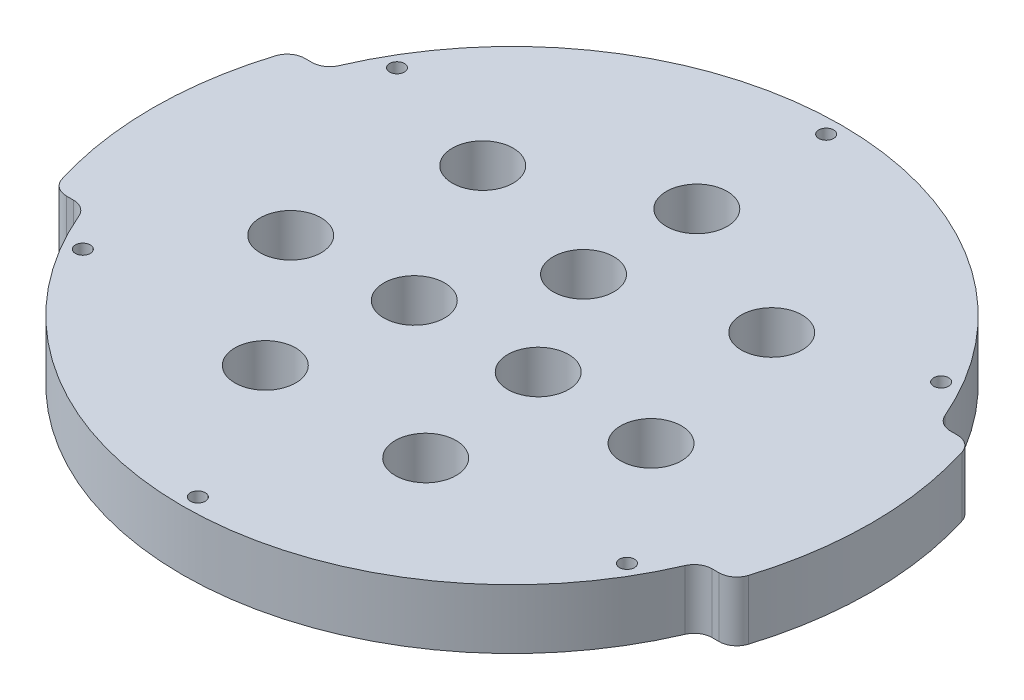
SolidWorks part; units mm, degrees
ref_plane "前视" through (0, 0, 0) normal (0, 0, 1) x (1, 0, 0)
ref_plane "上视" through (0, 0, 0) normal (0, 1, 0) x (1, 0, 0)
ref_plane "右视" through (0, 0, 0) normal (1, 0, 0) x (0, 0, -1)
sketch "草图3" plane through (0, 0, 0) normal (0, 1, 0) x (1, 0, 0)
  circle A0 centre (0, 0) radius 60.3
extrude "凸台-拉伸2" add sketch "草图3" along normal blind 10
sketch "草图4" plane through (0, 10, 0) normal (0, 1, 0) x (1, 0, 0)
  line L0 (-75.2656, 20) -> (82.2187, 20) construction
  line L1 (80.5383, -20) -> (-108.875, -20) construction
  line L2 (-51.5567, 20) -> (-56.8866, 20)
  line L3 (51.5567, 20) -> (56.8866, 20)
  line L4 (-56.8866, -20) -> (-51.5567, -20)
  line L5 (51.5567, -20) -> (56.8866, -20)
  arc A0 (51.5567, 20) -> (-51.5567, 20) centre (0, 0) ccw
  arc A1 (56.8866, 20) -> (-56.8866, 20) centre (0, 0) ccw
  circle A2 centre (0, 0) radius 60.3 construction
  arc A3 (-51.5567, -20) -> (51.5567, -20) centre (0, 0) ccw
  arc A4 (-56.8866, -20) -> (56.8866, -20) centre (0, 0) ccw
  dimension "D1" = 20
  dimension "D2" = 20
extrude "切除-拉伸2" cut sketch "草图4" against normal through all
fillet "圆角1" radius 3 8 edges at (51.5567, 5, -20) (56.8866, 5, -20) (56.8866, 5, 20) (51.5567, 5, 20) (-51.5567, 5, 20) (-56.8866, 5, 20) (-56.8866, 5, -20) (-51.5567, 5, -20)
sketch "草图5" plane through (0, 0, 0) normal (0, -1, 0) x (1, 0, 0)
  circle A0 centre (0, -52.7) radius 1.25
  arc A1 (-50.8147, -21.8165) -> (50.8147, -21.8165) centre (0, 0) ccw construction
  circle A2 centre (-45.6395, -26.35) radius 1.25
  circle A3 centre (-45.6395, 26.35) radius 1.25
  circle A4 centre (0, 52.7) radius 1.25
  circle A5 centre (45.6395, 26.35) radius 1.25
  circle A6 centre (45.6395, -26.35) radius 1.25
  point P2 (0, -55.3)
  point P19 (0, 0)
  dimension "D2" = 2.5
  dimension "D1" = 2.6
  dimension "D3" = 6
extrude "切除-拉伸3" cut sketch "草图5" against normal through all
sketch "草图6" plane through (0, 10, 0) normal (0, 1, 0) x (1, 0, 0)
  circle A0 centre (0, 31) radius 5.1
  circle A1 centre (24.2368, 19.3282) radius 5.1
  circle A2 centre (30.2228, -6.8981) radius 5.1
  circle A3 centre (13.4504, -27.93) radius 5.1
  circle A4 centre (-13.4504, -27.93) radius 5.1
  circle A5 centre (-30.2228, -6.8981) radius 5.1
  circle A6 centre (-24.2368, 19.3282) radius 5.1
  point P18 (0, 0)
  dimension "D1" = 31
  dimension "D2" = 7
extrude "切除-拉伸4" cut sketch "草图6" against normal through all
sketch "草图7" plane through (0, 10, 0) normal (0, 1, 0) x (1, 0, 0)
  circle A0 centre (0, 12) radius 5.1
  circle A1 centre (10.3923, -6) radius 5.1
  circle A2 centre (-10.3923, -6) radius 5.1
  point P10 (0, 0)
  dimension "D1" = 12
  dimension "D2" = 3
extrude "切除-拉伸5" cut sketch "草图7" against normal through all
